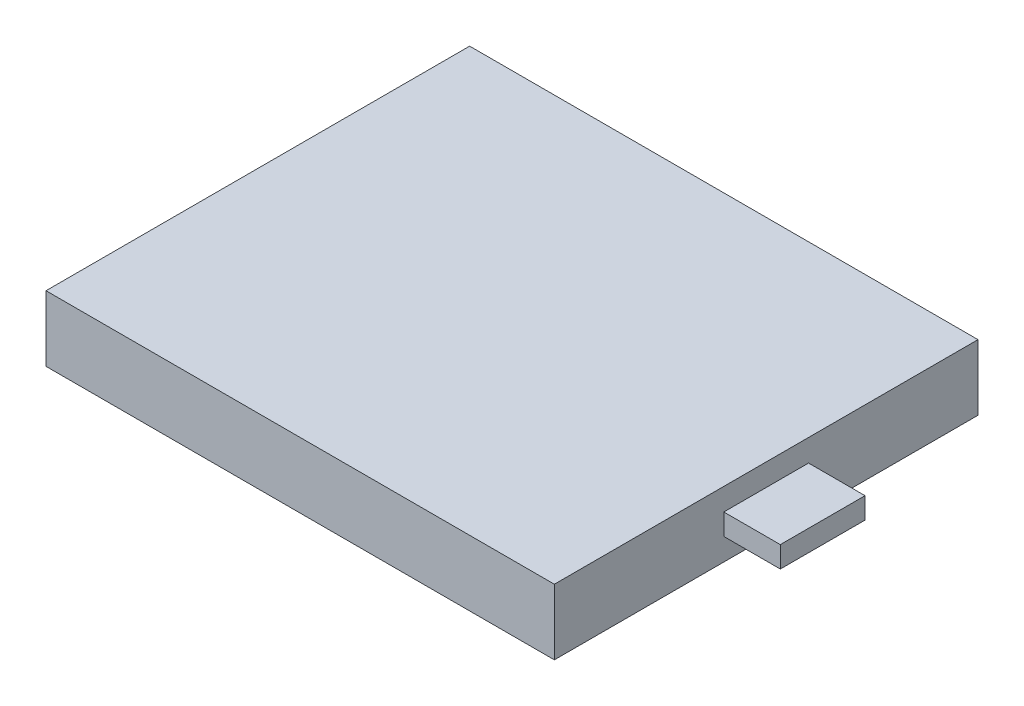
SolidWorks part; units mm, degrees
ref_plane "Front Plane" through (0, 0, 0) normal (0, 0, 1) x (1, 0, 0)
ref_plane "Top Plane" through (0, 0, 0) normal (0, 1, 0) x (1, 0, 0)
ref_plane "Right Plane" through (0, 0, 0) normal (1, 0, 0) x (0, 0, -1)
sketch "Sketch1" plane through (0, 0, 0) normal (0, 1, 0) x (1, 0, 0)
  line L1 (0, 0) -> (36, 0)
  line L2 (0, 0) -> (0, 30)
  line L3 (0, 30) -> (36, 30)
  line L4 (36, 0) -> (36, 30)
  dimension "D1" = 30
  dimension "D2" = 36
extrude "Boss-Extrude1" add sketch "Sketch1" along normal blind 4.64
sketch "Sketch2" plane through (36, 0, 0) normal (1, 0, 0) x (0, 0, -1)
  line L0 (15, 0) -> (15, 4.64) construction
  line L1 (0, 0) -> (30, 0) construction
  line L2 (0, 4.64) -> (30, 4.64) construction
  line L4 (12, 1.57) -> (18, 1.57)
  line L5 (12, 1.57) -> (12, 3.07)
  line L6 (12, 3.07) -> (18, 3.07)
  line L7 (18, 1.57) -> (18, 3.07)
  line L8 (12, 1.57) -> (18, 3.07) construction
  line L9 (12, 3.07) -> (18, 1.57) construction
  point P6 (15, 2.32)
  dimension "D1" = 6
  dimension "D2" = 1.5
extrude "Boss-Extrude2" add sketch "Sketch2" along normal blind 4 contours L6 L7 L4 L5
